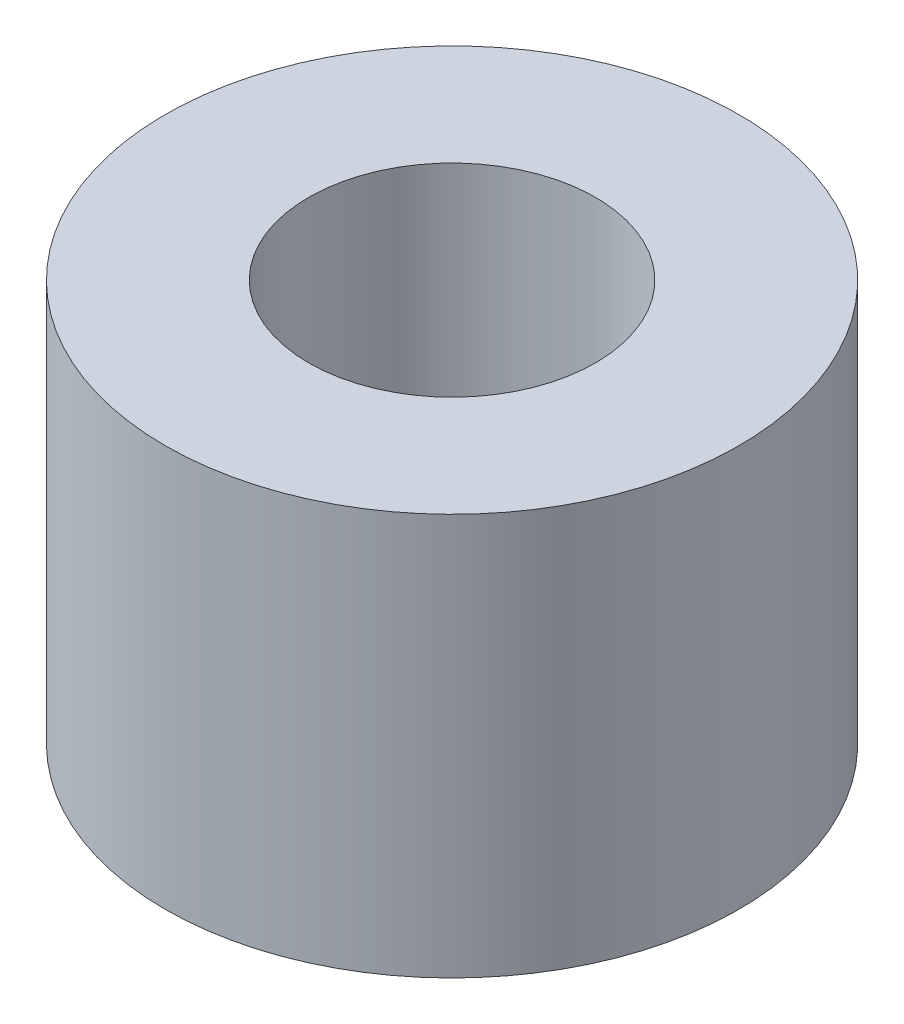
SolidWorks part; units mm, degrees
ref_plane "Front Plane" through (0, 0, 0) normal (0, 0, 1) x (1, 0, 0)
ref_plane "Top Plane" through (0, 0, 0) normal (0, 1, 0) x (1, 0, 0)
ref_plane "Right Plane" through (0, 0, 0) normal (1, 0, 0) x (0, 0, -1)
sketch "Sketch9" plane through (0, 0, 0) normal (0, 1, 0) x (1, 0, 0)
  circle A0 centre (0, 0) radius 2
  circle A1 centre (0, 0) radius 4
  dimension "D1" = 8
  dimension "D2" = 4
extrude "Boss-Extrude6" add sketch "Sketch9" along normal blind 5.6
